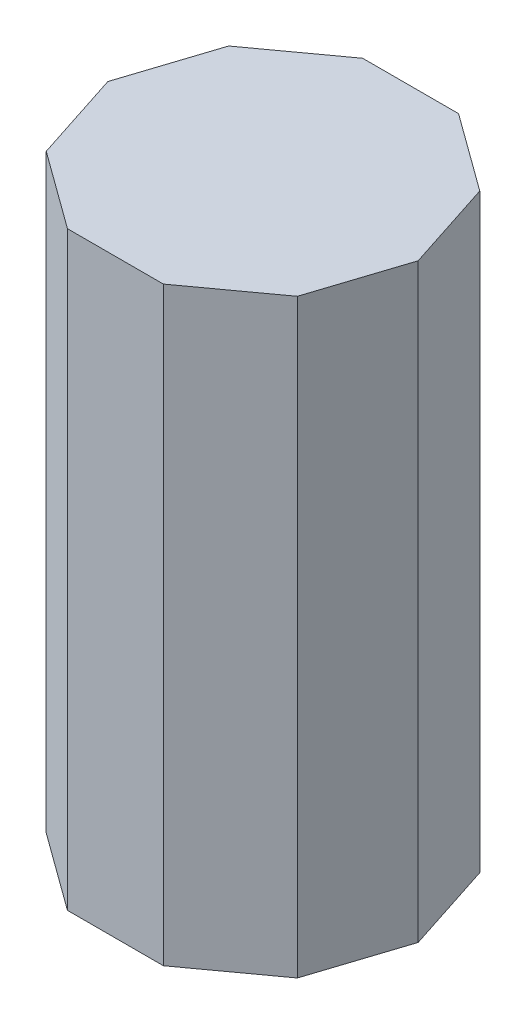
SolidWorks part; units mm, degrees
ref_plane "Front" through (0, 0, 0) normal (0, 0, 1) x (1, 0, 0)
ref_plane "Top" through (0, 0, 0) normal (0, 1, 0) x (1, 0, 0)
ref_plane "Right" through (0, 0, 0) normal (1, 0, 0) x (0, 0, -1)
sketch "Sketch1" plane through (0, 0, 0) normal (0, 1, 0) x (1, 0, 0)
  line L1 (4.2533, -3.0902) -> (5.2573, 0)
  line L2 (5.2573, 0) -> (4.2533, 3.0902)
  line L3 (4.2533, 3.0902) -> (1.6246, 5)
  line L4 (1.6246, 5) -> (-1.6246, 5)
  line L5 (-1.6246, 5) -> (-4.2533, 3.0902)
  line L6 (-4.2533, 3.0902) -> (-5.2573, 0)
  line L7 (-5.2573, 0) -> (-4.2533, -3.0902)
  line L8 (-4.2533, -3.0902) -> (-1.6246, -5)
  line L9 (-1.6246, -5) -> (1.6246, -5)
  line L10 (1.6246, -5) -> (4.2533, -3.0902)
  circle A0 centre (0, 0) radius 5 construction
  dimension "D1" = 10
extrude "Extrude1" add sketch "Sketch1" along normal blind 20
